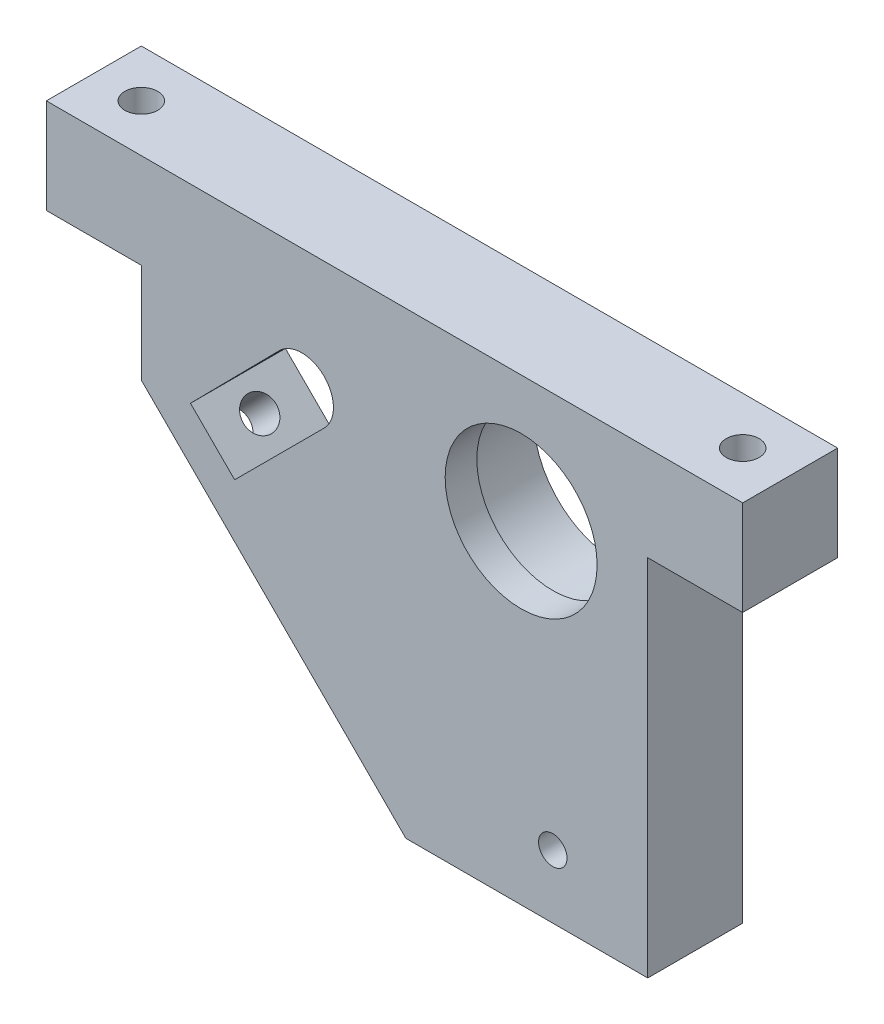
SolidWorks part; units mm, degrees
ref_plane "前视基准面" through (0, 0, 0) normal (0, 0, 1) x (1, 0, 0)
ref_plane "上视基准面" through (0, 0, 0) normal (0, 1, 0) x (1, 0, 0)
ref_plane "右视基准面" through (0, 0, 0) normal (1, 0, 0) x (0, 0, -1)
sketch "草图1" plane through (0, 0, 0) normal (0, 0, 1) x (1, 0, 0)
  line L0 (-33.801, 26.4292) -> (-27.4406, 26.4292)
  line L1 (-33.801, 41.4292) -> (56.199, 41.4292)
  line L2 (-33.801, 41.4292) -> (-33.801, 26.4292)
  line L3 (22.9883, -31.0708) -> (61.199, -31.0708)
  line L5 (-18.801, 10.7185) -> (22.9883, -31.0708)
  line L7 (-28.6561, -13.0706) -> (32.4644, 48.05) construction
  line L8 (-11.035, 11.4378) -> (2.9923, 25.6488)
  line L9 (6.5876, -21.0708) -> (83.4627, -21.0708) construction
  line L10 (-4.0559, 4.4587) -> (10.0635, 18.5781)
  line L11 (46.199, -4.7233) -> (46.199, -58.0817) construction
  line L12 (-27.4406, 26.4292) -> (-18.801, 26.4292)
  line L13 (-18.801, 26.4292) -> (-18.801, 10.7185)
  line L14 (56.199, 41.4292) -> (76.199, 41.4292)
  line L15 (76.199, 41.4292) -> (76.199, 26.4292)
  line L16 (76.199, 26.4292) -> (61.199, 26.4292)
  line L17 (61.199, 26.4292) -> (61.199, -31.0708)
  line L19 (-11.035, 11.4378) -> (-4.0559, 4.4587)
  circle A0 centre (41.199, 21.4292) radius 12
  circle A1 centre (41.199, 21.4292) radius 25 construction
  arc A3 (10.0635, 18.5781) -> (2.9923, 25.6488) centre (6.5508, 22.1363) ccw
  circle A4 centre (46.199, -21.0708) radius 2.25
  dimension "D3" = 50
  dimension "D4" = 24
  dimension "D5" = 20
  dimension "D6" = 20
  dimension "D8" = 50
  dimension "D13" = 6
  dimension "D14" = 5
  dimension "D15" = 20
  dimension "D17" = 4.5
  dimension "D7" = 45
  dimension "D9" = 15
  dimension "D10" = 15
  dimension "D11" = 45
  dimension "D12" = 25
  dimension "D16" = 10
  dimension "D18" = 15
  dimension "D19" = 15
  dimension "D20" = 15
  dimension "D21" = 110
  dimension "D22" = 72.5
extrude "凸台-拉伸1" add sketch "草图1" along normal blind 15
sketch "草图2" plane through (0, 0, 0) normal (0, 0, -1) x (-1, 0, 0)
  circle A0 centre (-41.199, 21.4292) radius 13
  dimension "D1" = 26
extrude "切除-拉伸1" cut sketch "草图2" against normal blind 10
sketch "草图3" plane through (0, 41.4292, 0) normal (0, 1, 0) x (1, 0, 0)
  line L0 (-45.1664, -7.5) -> (87.6779, -7.5) construction
  line L1 (76.199, 0) -> (-33.801, 0) construction
  line L2 (76.199, -15) -> (-33.801, -15) construction
  line L3 (-33.801, -15) -> (-33.801, 0) construction
  line L4 (76.199, -15) -> (76.199, 0) construction
  circle A0 centre (-26.301, -7.5) radius 2.6
  circle A1 centre (68.699, -7.5) radius 2.6
  dimension "D1" = 5.2
  dimension "D2" = 7.5
  dimension "D3" = 7.5
extrude "切除-拉伸2" cut sketch "草图3" against normal through all
sketch "草图5" plane through (-4.0412, -4.0412, 0) normal (-0.7071, -0.7071, 0) x (0, 0, 1)
  line L0 (-9.1574, 11.0234) -> (29.9899, 11.0234) construction
  line L1 (7.5, 30.0407) -> (7.5, -16.3526) construction
  line L2 (0, 20.8734) -> (0, -38.2256) construction
  line L3 (15, 20.8734) -> (15, -38.2256) construction
  line L4 (15, 20.8734) -> (0, 20.8734) construction
  circle A0 centre (7.5, 11.0234) radius 2.6
  dimension "D2" = 5.2
  dimension "D1" = 9.85
extrude "切除-拉伸3" cut sketch "草图5" against normal blind 10
